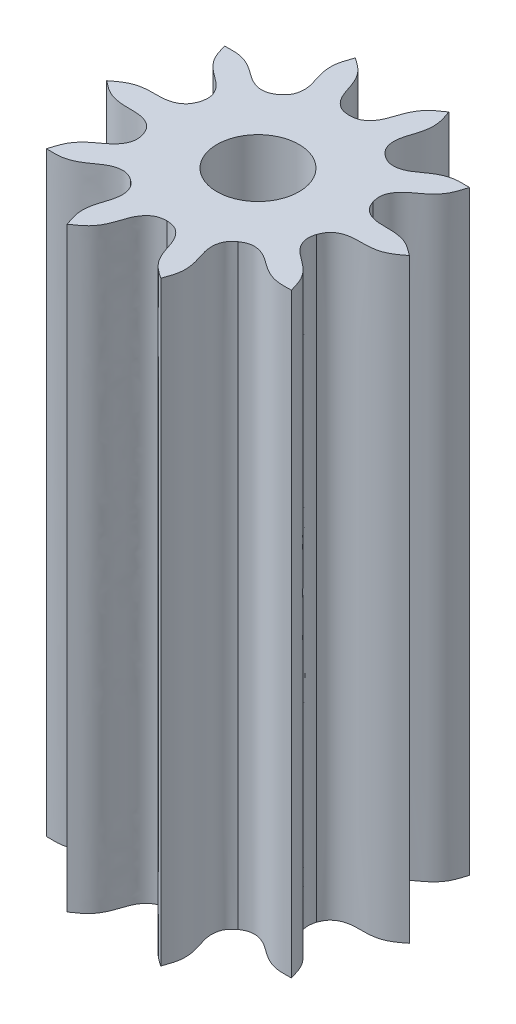
SolidWorks part; units mm, degrees
ref_plane "Alzado" through (0, 0, 0) normal (0, 0, 1) x (1, 0, 0)
ref_plane "Planta" through (0, 0, 0) normal (0, 1, 0) x (1, 0, 0)
ref_plane "Vista lateral" through (0, 0, 0) normal (1, 0, 0) x (0, 0, -1)
sketch "Sketch1" plane through (0, 0, 0) normal (0, 1, 0) x (1, 0, 0)
  line L0 (-1000, 0) -> (49000, 0) construction
  line L1 (0, -1000) -> (0, 49000) construction
  line L2 (0, 0) -> (15450.8497, 47552.8258) construction
  circle A0 centre (0, 0) radius 0.3 construction
  circle A1 centre (0, 0) radius 0.4981 construction
  circle A2 centre (0, 0) radius 0.135
  spline S0 degree 3 poles (0, 0.3) (-0.008, 0.3006) (-0.0237, 0.3018) (-0.0454, 0.3142) (-0.0625, 0.3349) (-0.0751, 0.3643) (-0.0854, 0.401) (-0.1089, 0.4433) (-0.1377, 0.4628) (-0.1539, 0.4738) knots 0 0 0 0 0.097339 0.191381 0.295712 0.422744 0.578988 0.764031 1 1 1 1
  spline S1 degree 3 poles (0.1763, 0.2427) (0.1702, 0.2479) (0.1582, 0.2581) (0.148, 0.2808) (0.1463, 0.3077) (0.1534, 0.3388) (0.1666, 0.3746) (0.1725, 0.4226) (0.1606, 0.4554) (0.1539, 0.4738) knots 0 0 0 0 0.097339 0.191381 0.295712 0.422744 0.578988 0.764031 1 1 1 1
  spline S2 degree 3 poles (0.1763, 0.2427) (0.1832, 0.2385) (0.1966, 0.2302) (0.2214, 0.2275) (0.2475, 0.2342) (0.2749, 0.2506) (0.3047, 0.2742) (0.3487, 0.2947) (0.3835, 0.2935) (0.403, 0.2928) knots 0 0 0 0 0.097339 0.191381 0.295712 0.422744 0.578988 0.764031 1 1 1 1
  spline S3 degree 3 poles (0.2853, 0.0927) (0.2834, 0.1005) (0.2797, 0.1158) (0.2848, 0.1402) (0.2992, 0.163) (0.3233, 0.184) (0.355, 0.2051) (0.388, 0.2405) (0.3976, 0.274) (0.403, 0.2928) knots 0 0 0 0 0.097339 0.191381 0.295712 0.422744 0.578988 0.764031 1 1 1 1
  spline S4 degree 3 poles (0.2853, 0.0927) (0.2884, 0.0853) (0.2944, 0.0707) (0.3128, 0.0539) (0.3379, 0.044) (0.3697, 0.0412) (0.4077, 0.0427) (0.4553, 0.0335) (0.4827, 0.012) (0.4981, 0) knots 0 0 0 0 0.097339 0.191381 0.295712 0.422744 0.578988 0.764031 1 1 1 1
  spline S5 degree 3 poles (0.2853, -0.0927) (0.2884, -0.0853) (0.2944, -0.0707) (0.3128, -0.0539) (0.3379, -0.044) (0.3697, -0.0412) (0.4077, -0.0427) (0.4553, -0.0335) (0.4827, -0.012) (0.4981, 0) knots 0 0 0 0 0.097339 0.191381 0.295712 0.422744 0.578988 0.764031 1 1 1 1
  spline S6 degree 3 poles (0.2853, -0.0927) (0.2834, -0.1005) (0.2797, -0.1158) (0.2848, -0.1402) (0.2992, -0.163) (0.3233, -0.184) (0.355, -0.2051) (0.388, -0.2405) (0.3976, -0.274) (0.403, -0.2928) knots 0 0 0 0 0.097339 0.191381 0.295712 0.422744 0.578988 0.764031 1 1 1 1
  spline S7 degree 3 poles (0.1763, -0.2427) (0.1832, -0.2385) (0.1966, -0.2302) (0.2214, -0.2275) (0.2475, -0.2342) (0.2749, -0.2506) (0.3047, -0.2742) (0.3487, -0.2947) (0.3835, -0.2935) (0.403, -0.2928) knots 0 0 0 0 0.097339 0.191381 0.295712 0.422744 0.578988 0.764031 1 1 1 1
  spline S8 degree 3 poles (0, 0.3) (0.008, 0.3006) (0.0237, 0.3018) (0.0454, 0.3142) (0.0625, 0.3349) (0.0751, 0.3643) (0.0854, 0.401) (0.1089, 0.4433) (0.1377, 0.4628) (0.1539, 0.4738) knots 0 0 0 0 0.097339 0.191381 0.295712 0.422744 0.578988 0.764031 1 1 1 1
  spline S9 degree 3 poles (0.1763, -0.2427) (0.1702, -0.2479) (0.1582, -0.2581) (0.148, -0.2808) (0.1463, -0.3077) (0.1534, -0.3388) (0.1666, -0.3746) (0.1725, -0.4226) (0.1606, -0.4554) (0.1539, -0.4738) knots 0 0 0 0 0.097339 0.191381 0.295712 0.422744 0.578988 0.764031 1 1 1 1
  spline S10 degree 3 poles (0, -0.3) (0.008, -0.3006) (0.0237, -0.3018) (0.0454, -0.3142) (0.0625, -0.3349) (0.0751, -0.3643) (0.0854, -0.401) (0.1089, -0.4433) (0.1377, -0.4628) (0.1539, -0.4738) knots 0 0 0 0 0.097339 0.191381 0.295712 0.422744 0.578988 0.764031 1 1 1 1
  spline S11 degree 3 poles (0, -0.3) (-0.008, -0.3006) (-0.0237, -0.3018) (-0.0454, -0.3142) (-0.0625, -0.3349) (-0.0751, -0.3643) (-0.0854, -0.401) (-0.1089, -0.4433) (-0.1377, -0.4628) (-0.1539, -0.4738) knots 0 0 0 0 0.097339 0.191381 0.295712 0.422744 0.578988 0.764031 1 1 1 1
  spline S12 degree 3 poles (-0.1763, -0.2427) (-0.1702, -0.2479) (-0.1582, -0.2581) (-0.148, -0.2808) (-0.1463, -0.3077) (-0.1534, -0.3388) (-0.1666, -0.3746) (-0.1725, -0.4226) (-0.1606, -0.4554) (-0.1539, -0.4738) knots 0 0 0 0 0.097339 0.191381 0.295712 0.422744 0.578988 0.764031 1 1 1 1
  spline S13 degree 3 poles (-0.1763, -0.2427) (-0.1832, -0.2385) (-0.1966, -0.2302) (-0.2214, -0.2275) (-0.2475, -0.2342) (-0.2749, -0.2506) (-0.3047, -0.2742) (-0.3487, -0.2947) (-0.3835, -0.2935) (-0.403, -0.2928) knots 0 0 0 0 0.097339 0.191381 0.295712 0.422744 0.578988 0.764031 1 1 1 1
  spline S14 degree 3 poles (-0.2853, -0.0927) (-0.2834, -0.1005) (-0.2797, -0.1158) (-0.2848, -0.1402) (-0.2992, -0.163) (-0.3233, -0.184) (-0.355, -0.2051) (-0.388, -0.2405) (-0.3976, -0.274) (-0.403, -0.2928) knots 0 0 0 0 0.097339 0.191381 0.295712 0.422744 0.578988 0.764031 1 1 1 1
  spline S15 degree 3 poles (-0.2853, -0.0927) (-0.2884, -0.0853) (-0.2944, -0.0707) (-0.3128, -0.0539) (-0.3379, -0.044) (-0.3697, -0.0412) (-0.4077, -0.0427) (-0.4553, -0.0335) (-0.4827, -0.012) (-0.4981, 0) knots 0 0 0 0 0.097339 0.191381 0.295712 0.422744 0.578988 0.764031 1 1 1 1
  spline S16 degree 3 poles (-0.2853, 0.0927) (-0.2884, 0.0853) (-0.2944, 0.0707) (-0.3128, 0.0539) (-0.3379, 0.044) (-0.3697, 0.0412) (-0.4077, 0.0427) (-0.4553, 0.0335) (-0.4827, 0.012) (-0.4981, 0) knots 0 0 0 0 0.097339 0.191381 0.295712 0.422744 0.578988 0.764031 1 1 1 1
  spline S17 degree 3 poles (-0.2853, 0.0927) (-0.2834, 0.1005) (-0.2797, 0.1158) (-0.2848, 0.1402) (-0.2992, 0.163) (-0.3233, 0.184) (-0.355, 0.2051) (-0.388, 0.2405) (-0.3976, 0.274) (-0.403, 0.2928) knots 0 0 0 0 0.097339 0.191381 0.295712 0.422744 0.578988 0.764031 1 1 1 1
  spline S18 degree 3 poles (-0.1763, 0.2427) (-0.1832, 0.2385) (-0.1966, 0.2302) (-0.2214, 0.2275) (-0.2475, 0.2342) (-0.2749, 0.2506) (-0.3047, 0.2742) (-0.3487, 0.2947) (-0.3835, 0.2935) (-0.403, 0.2928) knots 0 0 0 0 0.097339 0.191381 0.295712 0.422744 0.578988 0.764031 1 1 1 1
  spline S19 degree 3 poles (-0.1763, 0.2427) (-0.1702, 0.2479) (-0.1582, 0.2581) (-0.148, 0.2808) (-0.1463, 0.3077) (-0.1534, 0.3388) (-0.1666, 0.3746) (-0.1725, 0.4226) (-0.1606, 0.4554) (-0.1539, 0.4738) knots 0 0 0 0 0.097339 0.191381 0.295712 0.422744 0.578988 0.764031 1 1 1 1
  point P163 (0, 0)
  dimension "D2" = 0.6
  dimension "D3" = 0.9963
  dimension "D4" = 0.27
  dimension "D1" = 18
extrude "Boss-Extrude1" add sketch "Sketch1" along normal blind 1.96
